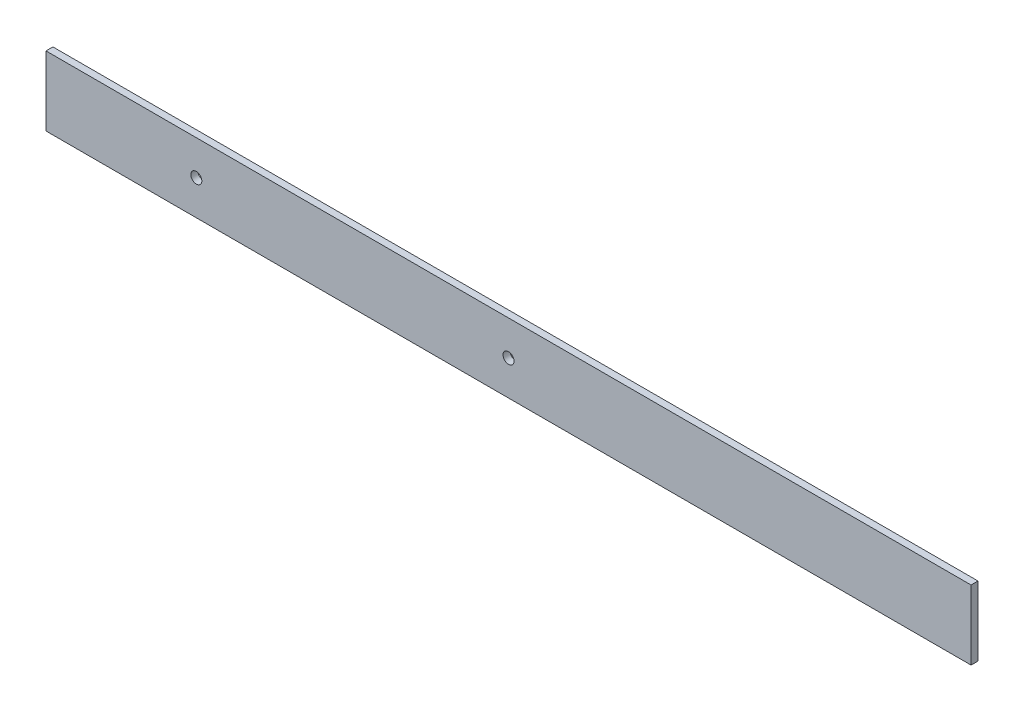
SolidWorks part; units mm, degrees
material "Balsa"
ref_plane "Alzado" through (0, 0, 0) normal (0, 0, 1) x (1, 0, 0)
ref_plane "Planta" through (0, 0, 0) normal (0, 1, 0) x (1, 0, 0)
ref_plane "Vista lateral" through (0, 0, 0) normal (1, 0, 0) x (0, 0, -1)
sketch "Croquis1" plane through (0, 0, 0) normal (0, 0, 1) x (1, 0, 0)
  line L1 (-200, 15) -> (200, 15)
  line L2 (-200, 15) -> (-200, -15)
  line L3 (-200, -15) -> (200, -15)
  line L4 (200, 15) -> (200, -15)
  line L5 (-200, 15) -> (200, -15) construction
  line L6 (-200, -15) -> (200, 15) construction
  circle A0 centre (0, 0) radius 2.3813
  point P0 (0, 0)
  dimension "D3" = 4.7625
  dimension "D1" = 400
  dimension "D2" = 30
extrude "Saliente-Extruir1" add sketch "Croquis1" along normal blind 3
sketch "Croquis2" plane through (0, 0, 0) normal (0, 0, 1) x (1, 0, 0)
  line L0 (-135, 15) -> (-135, -15) construction
  line L1 (200, 15) -> (-200, 15) construction
  line L2 (-200, -15) -> (200, -15) construction
  line L3 (-200, 15) -> (-200, -15) construction
  line L4 (-200, 0) -> (-143.4148, 0) construction
  circle A0 centre (-135, 0) radius 2.3813
  circle A1 centre (0, 0) radius 2.3813 construction
  dimension "D2" = 4.7625
  dimension "D1" = 135
extrude "Cortar-Extruir2" cut sketch "Croquis2" along normal through all
